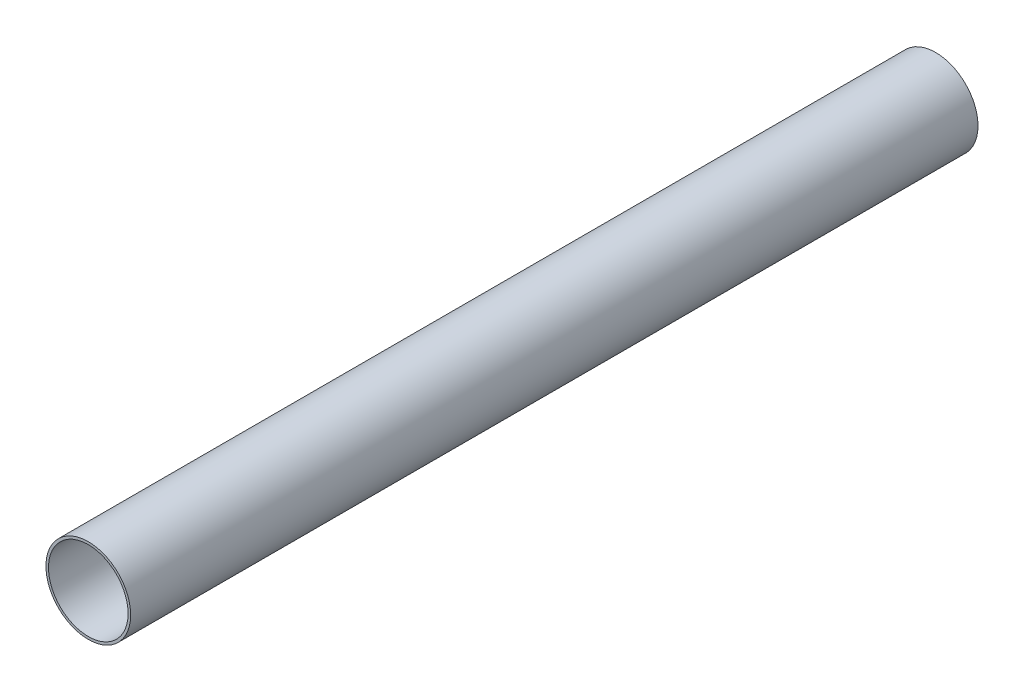
SolidWorks part; units mm, degrees
material "6061-T6 (SS)"
ref_plane "Front Plane" through (0, 0, 0) normal (0, 0, 1) x (1, 0, 0)
ref_plane "Top Plane" through (0, 0, 0) normal (0, 1, 0) x (1, 0, 0)
ref_plane "Right Plane" through (0, 0, 0) normal (1, 0, 0) x (0, 0, -1)
sketch "Sketch1" plane through (0, 0, 0) normal (0, 0, 1) x (1, 0, 0)
  circle A0 centre (0, 0) radius 25
  circle A1 centre (0, 0) radius 23.5
extrude "Boss-Extrude1" add sketch "Sketch1" along normal blind 500
